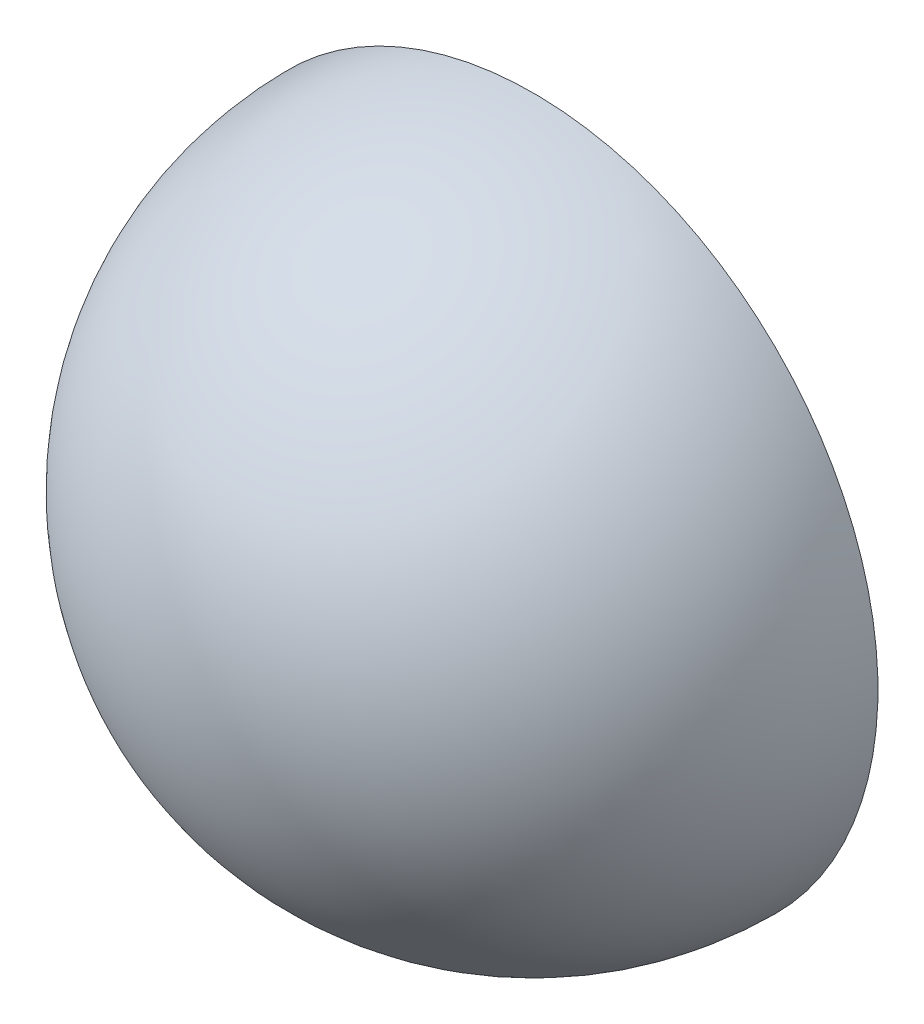
SolidWorks part; units mm, degrees
ref_plane "Front Plane" through (0, 0, 0) normal (0, 0, 1) x (1, 0, 0)
ref_plane "Top Plane" through (0, 0, 0) normal (0, 1, 0) x (1, 0, 0)
ref_plane "Right Plane" through (0, 0, 0) normal (1, 0, 0) x (0, 0, -1)
sketch "Sketch1" plane through (0, 0, 0) normal (0, 0, 1) x (1, 0, 0)
  line L1 (-120, 0) -> (-119, 0)
  line L3 (-1, 0) -> (0, 0)
  line L4 (-119, 0) -> (-1, 0) construction
  arc A0 (-120, 0) -> (0, 0) centre (-60, 0) cw
  arc A1 (-119, 0) -> (-1, 0) centre (-60, 0) cw
  dimension "D1" = 120
  dimension "D2" = 1
revolve "Revolve1" add sketch "Sketch1" angle 180 about L4
